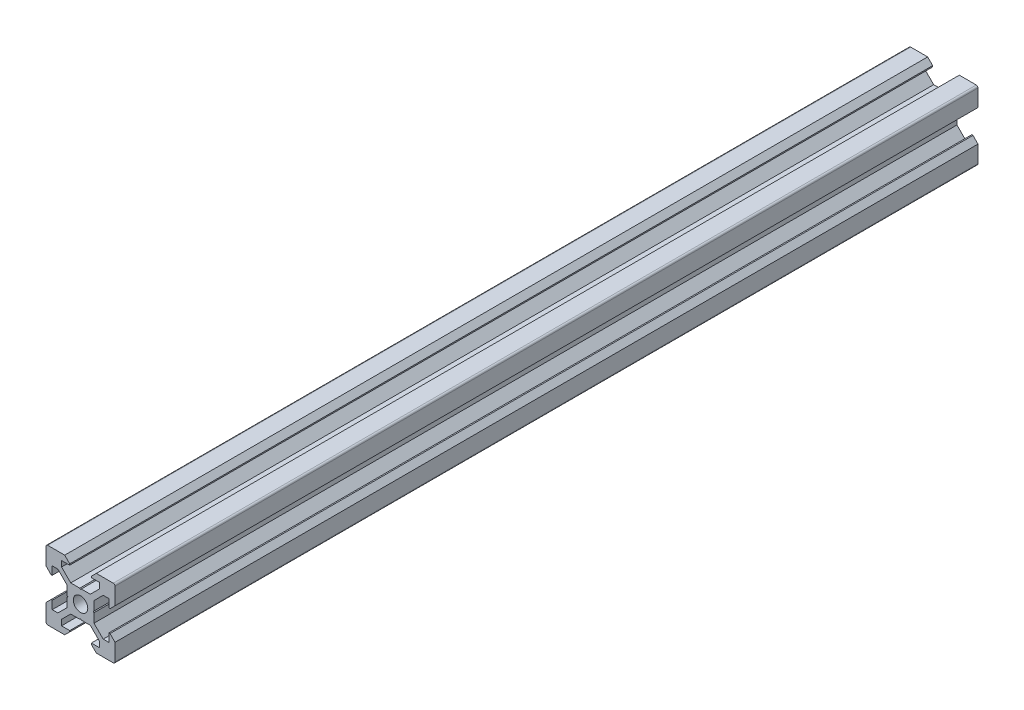
SolidWorks part; units mm, degrees
material "6061-T6 (SS)"
ref_plane "Front Plane" through (0, 0, 0) normal (0, 0, 1) x (1, 0, 0)
ref_plane "Top Plane" through (0, 0, 0) normal (0, 1, 0) x (1, 0, 0)
ref_plane "Right Plane" through (0, 0, 0) normal (1, 0, 0) x (0, 0, -1)
sketch "Sketch1" plane through (0, 0, 0) normal (0, 0, 1) x (1, 0, 0)
  line L1 (9.5, -10) -> (-9.5, -10)
  line L2 (10, -9.5) -> (10, 9.5)
  line L3 (9.5, 10) -> (-9.5, 10)
  line L4 (-10, -9.5) -> (-10, 9.5)
  line L5 (10, -10) -> (-10, 10) construction
  line L6 (10, 10) -> (-10, -10) construction
  circle A0 centre (0, 0) radius 2.1
  arc A1 (-9.5, 10) -> (-10, 9.5) centre (-9.5, 9.5) ccw
  arc A2 (10, 9.5) -> (9.5, 10) centre (9.5, 9.5) ccw
  arc A3 (9.5, -10) -> (10, -9.5) centre (9.5, -9.5) ccw
  arc A4 (-9.5, -10) -> (-10, -9.5) centre (-9.5, -9.5) cw
  point P0 (0, 0)
  line B0 (0, 0) -> (0, 10) construction
  line B1 (0, 3.69) -> (-0.21, 3.9)
  line B2 (-0.21, 3.9) -> (-2.8393, 3.9)
  line B3 (-2.8393, 3.9) -> (-5.5, 6.5607)
  line B4 (-5.5, 6.5607) -> (-5.5, 8.2)
  line B5 (-5.5, 8.2) -> (-3.125, 8.2)
  line B6 (-3.125, 8.2) -> (-3.125, 8.545)
  line B7 (-3.125, 8.545) -> (-4.58, 10)
  line B8 (-4.58, 10) -> (4.58, 10)
  line B9 (0, 0) -> (-5.9132, 5.9132) construction
  line B10 (3.125, 8.545) -> (4.58, 10)
  line B11 (3.125, 8.2) -> (3.125, 8.545)
  line B12 (5.5, 8.2) -> (3.125, 8.2)
  line B13 (5.5, 6.5607) -> (5.5, 8.2)
  line B14 (2.8393, 3.9) -> (5.5, 6.5607)
  line B15 (0.21, 3.9) -> (2.8393, 3.9)
  line B16 (0, 3.69) -> (0.21, 3.9)
  line B17 (0, 0) -> (-10, 0) construction
  line B18 (-3.69, 0) -> (-3.9, -0.21)
  line B19 (-3.9, -0.21) -> (-3.9, -2.8393)
  line B20 (-3.9, -2.8393) -> (-6.5607, -5.5)
  line B21 (-6.5607, -5.5) -> (-8.2, -5.5)
  line B22 (-8.2, -5.5) -> (-8.2, -3.125)
  line B23 (-8.2, -3.125) -> (-8.545, -3.125)
  line B24 (-8.545, -3.125) -> (-10, -4.58)
  line B25 (-10, -4.58) -> (-10, 4.58)
  line B26 (0, 0) -> (-5.9132, -5.9132) construction
  line B27 (-8.545, 3.125) -> (-10, 4.58)
  line B28 (-8.2, 3.125) -> (-8.545, 3.125)
  line B29 (-8.2, 5.5) -> (-8.2, 3.125)
  line B30 (-6.5607, 5.5) -> (-8.2, 5.5)
  line B31 (-3.9, 2.8393) -> (-6.5607, 5.5)
  line B32 (-3.9, 0.21) -> (-3.9, 2.8393)
  line B33 (-3.69, 0) -> (-3.9, 0.21)
  line B34 (0, 0) -> (0, -10) construction
  line B35 (0, -3.69) -> (0.21, -3.9)
  line B36 (0.21, -3.9) -> (2.8393, -3.9)
  line B37 (2.8393, -3.9) -> (5.5, -6.5607)
  line B38 (5.5, -6.5607) -> (5.5, -8.2)
  line B39 (5.5, -8.2) -> (3.125, -8.2)
  line B40 (3.125, -8.2) -> (3.125, -8.545)
  line B41 (3.125, -8.545) -> (4.58, -10)
  line B42 (4.58, -10) -> (-4.58, -10)
  line B43 (0, 0) -> (5.9132, -5.9132) construction
  line B44 (-3.125, -8.545) -> (-4.58, -10)
  line B45 (-3.125, -8.2) -> (-3.125, -8.545)
  line B46 (-5.5, -8.2) -> (-3.125, -8.2)
  line B47 (-5.5, -6.5607) -> (-5.5, -8.2)
  line B48 (-2.8393, -3.9) -> (-5.5, -6.5607)
  line B49 (-0.21, -3.9) -> (-2.8393, -3.9)
  line B50 (0, -3.69) -> (-0.21, -3.9)
  line B51 (0, 0) -> (10, 0) construction
  line B52 (3.69, 0) -> (3.9, 0.21)
  line B53 (3.9, 0.21) -> (3.9, 2.8393)
  line B54 (3.9, 2.8393) -> (6.5607, 5.5)
  line B55 (6.5607, 5.5) -> (8.2, 5.5)
  line B56 (8.2, 5.5) -> (8.2, 3.125)
  line B57 (8.2, 3.125) -> (8.545, 3.125)
  line B58 (8.545, 3.125) -> (10, 4.58)
  line B59 (10, 4.58) -> (10, -4.58)
  line B60 (0, 0) -> (5.9132, 5.9132) construction
  line B61 (8.545, -3.125) -> (10, -4.58)
  line B62 (8.2, -3.125) -> (8.545, -3.125)
  line B63 (8.2, -5.5) -> (8.2, -3.125)
  line B64 (6.5607, -5.5) -> (8.2, -5.5)
  line B65 (3.9, -2.8393) -> (6.5607, -5.5)
  line B66 (3.9, -0.21) -> (3.9, -2.8393)
  line B67 (3.69, 0) -> (3.9, -0.21)
  dimension "D1" = 4.2
  dimension "D3" = 0.5
  dimension "D2" = 20
sketch_block_instance "V Slot 1-4"
sketch_block "V Slot 1" parameters "D1"=10, "D2"=11, "D3"=4.3, "D4"=1.8, "D5"=0.21, "D6"=45, "D7"=9.16, "D8"=1.5, "D9"=6.25
sketch_block_instance "V Slot 1-5"
sketch_block_instance "V Slot 1-6"
sketch_block_instance "V Slot 1-7"
extrude "Boss-Extrude1" add sketch "Sketch1" along normal blind 250 contours B67 B52 B53 B54 B55 B56 B57 B58 L2 A2 L3 B10 B11 B12 B13 B14 B15 B16 B1 B2 B3 B4 B5 B6 B7 A1 L4 B27 B28 B29 B30 B31 B32 B33 B18 B19 B20 B21 B22 B23 B24 A4 L1 B44 B45 B46 B47 B48 B49
